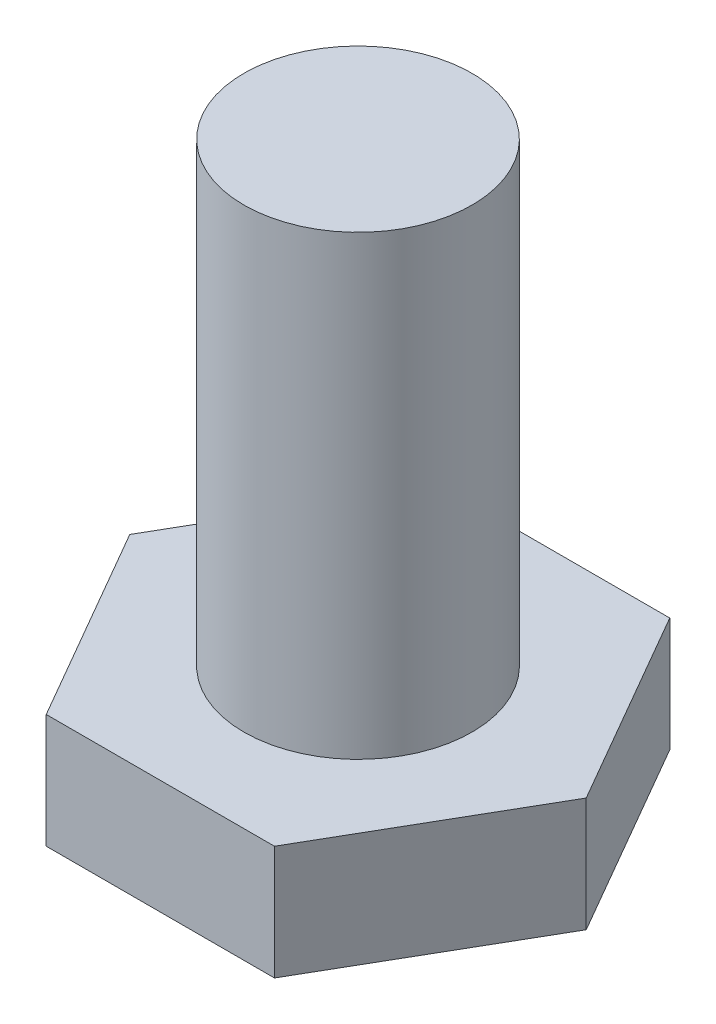
SolidWorks part; units mm, degrees
ref_plane "Front Plane" through (0, 0, 0) normal (0, 0, 1) x (1, 0, 0)
ref_plane "Top Plane" through (0, 0, 0) normal (0, 1, 0) x (1, 0, 0)
ref_plane "Right Plane" through (0, 0, 0) normal (1, 0, 0) x (0, 0, -1)
sketch "Sketch1" plane through (0, 0, 0) normal (0, 1, 0) x (1, 0, 0)
  line L1 (3, -5.1962) -> (6, 0)
  line L2 (6, 0) -> (3, 5.1962)
  line L3 (3, 5.1962) -> (-3, 5.1962)
  line L4 (-3, 5.1962) -> (-6, 0)
  line L5 (-6, 0) -> (-3, -5.1962)
  line L6 (-3, -5.1962) -> (3, -5.1962)
  circle A0 centre (0, 0) radius 5.1962 construction
  dimension "D1" = 6
extrude "Boss-Extrude1" add sketch "Sketch1" along normal blind 3
sketch "Sketch2" plane through (0, 3, 0) normal (0, 1, 0) x (1, 0, 0)
  circle A0 centre (0, 0) radius 3
  dimension "D1" = 6
extrude "Boss-Extrude2" add sketch "Sketch2" along normal blind 12
